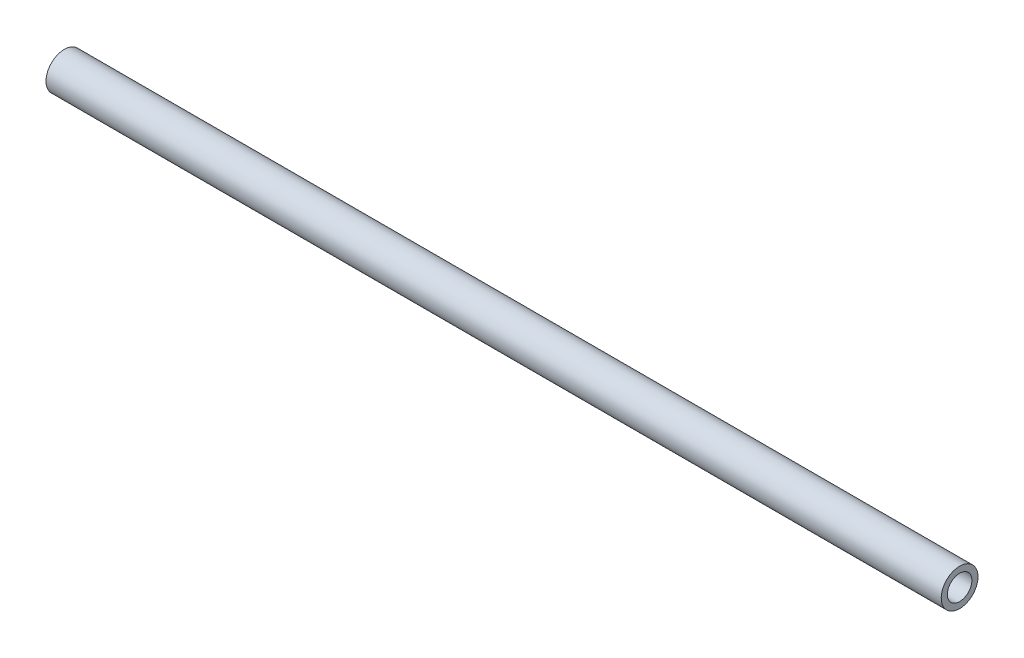
SolidWorks part; units mm, degrees
ref_plane "Front" through (0, 0, 0) normal (0, 0, 1) x (1, 0, 0)
ref_plane "Top" through (0, 0, 0) normal (0, 1, 0) x (1, 0, 0)
ref_plane "Right" through (0, 0, 0) normal (1, 0, 0) x (0, 0, -1)
sketch "Sketch1" plane through (0, 0, 0) normal (0, 0, 1) x (1, 0, 0)
  line L0 (231.775, 0) -> (-231.775, 0)
  point P4 (0, 0)
  dimension "D1" = 463.55
other "Round .75IN X .125IN SIDEWALL(1)"
ref_plane "Plane1" through (231.775, 0, 0) normal (-1, 0, 0) x (0, -1, 0)
sketch "Sketch13" plane through (231.775, 0, 0) normal (-1, 0, 0) x (0, -1, 0)
  circle A0 centre (0, 0) radius 6.35
  circle A1 centre (0, 0) radius 9.525
  point P5 (0, 0)
  dimension "D1" = 19.05
  dimension "D2" = 3.175
